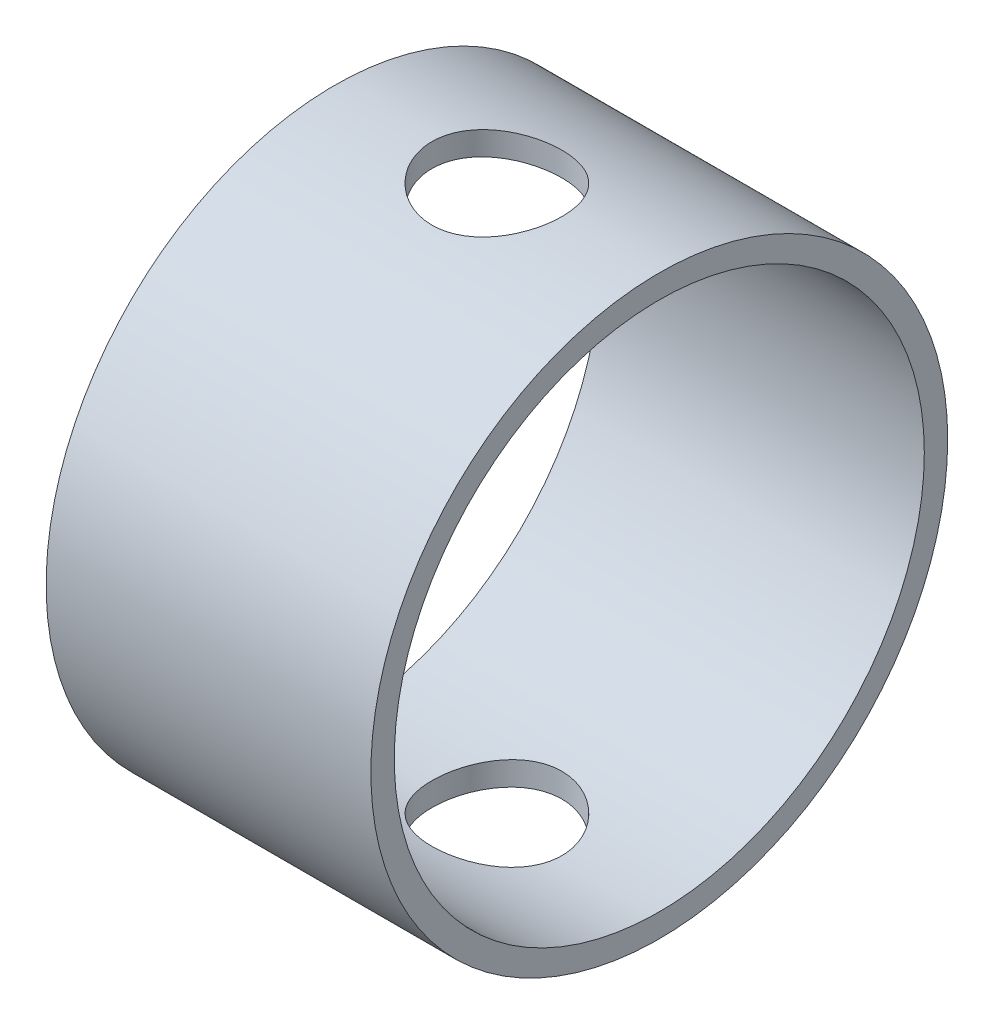
SolidWorks part; units mm, degrees
material "AISI 304"
ref_plane "Front Plane" through (0, 0, 0) normal (0, 0, 1) x (1, 0, 0)
ref_plane "Top Plane" through (0, 0, 0) normal (0, 1, 0) x (1, 0, 0)
ref_plane "Right Plane" through (0, 0, 0) normal (1, 0, 0) x (0, 0, -1)
sketch "Sketch1" plane through (0, 0, 0) normal (1, 0, 0) x (0, 0, -1)
  circle A0 centre (0, 0) radius 254
  circle A1 centre (0, 0) radius 233.4
  dimension "D1" = 508
  dimension "D2" = 466.8
extrude "Boss-Extrude1" add sketch "Sketch1" along normal blind 286
sketch "Sketch2" plane through (0, 0, 0) normal (0, 1, 0) x (1, 0, 0)
  line L0 (0, 0) -> (286, 0) construction
  line L1 (286, -254) -> (286, 254) construction
  circle A0 centre (143, 0) radius 57.25
  dimension "D1" = 114.5
extrude "Cut-Extrude1" cut sketch "Sketch2" against normal mid plane 546
